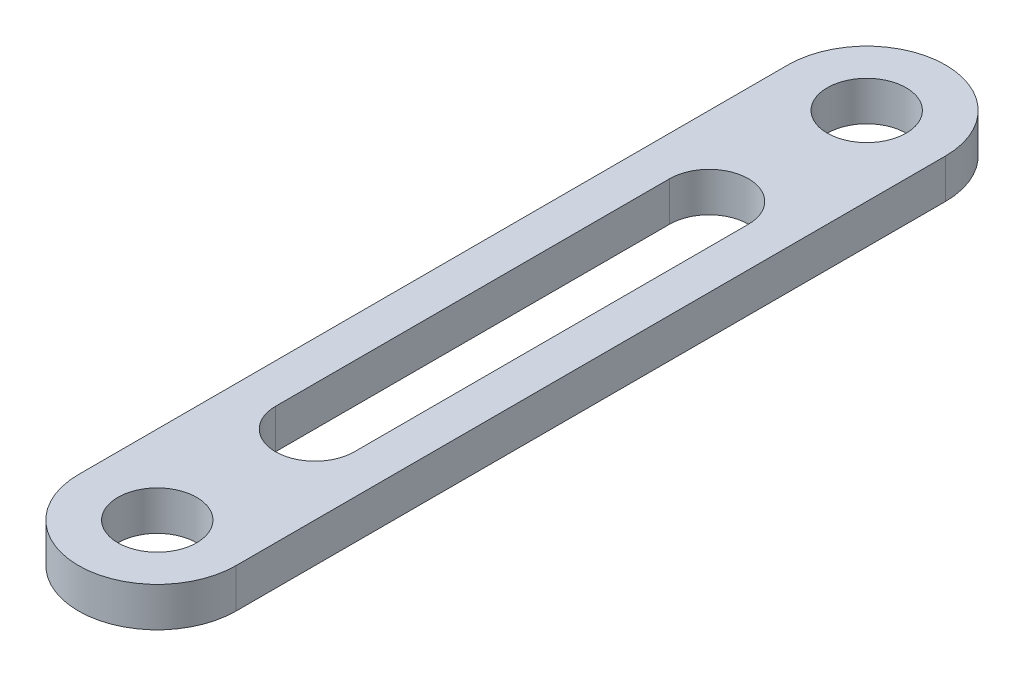
SolidWorks part; units mm, degrees
ref_plane "Front Plane" through (0, 0, 0) normal (0, 0, 1) x (1, 0, 0)
ref_plane "Top Plane" through (0, 0, 0) normal (0, 1, 0) x (1, 0, 0)
ref_plane "Right Plane" through (0, 0, 0) normal (1, 0, 0) x (0, 0, -1)
sketch "Sketch1" plane through (0, 0, 0) normal (0, 1, 0) x (1, 0, 0)
  line L0 (0, 0) -> (0, -90) construction
  line L1 (10, 0) -> (10, -90)
  line L2 (-10, 0) -> (-10, -90)
  line L3 (0, -20) -> (0, -70) construction
  line L4 (5, -20) -> (5, -70)
  line L5 (-5, -20) -> (-5, -70)
  arc A0 (10, 0) -> (-10, 0) centre (0, 0) ccw
  arc A1 (-10, -90) -> (10, -90) centre (0, -90) ccw
  arc A2 (5, -20) -> (-5, -20) centre (0, -20) ccw
  arc A3 (-5, -70) -> (5, -70) centre (0, -70) ccw
  circle A4 centre (0, 0) radius 5
  circle A5 centre (0, -90) radius 5
  point P3 (0, -45)
  point P10 (0, -45)
  dimension "D1" = 10
  dimension "D5" = 5
  dimension "D6" = 10
  dimension "D7" = 10
  dimension "D2" = 90
  dimension "D3" = 50
  dimension "D4" = 20
extrude "Boss-Extrude1" add sketch "Sketch1" along normal blind 5
